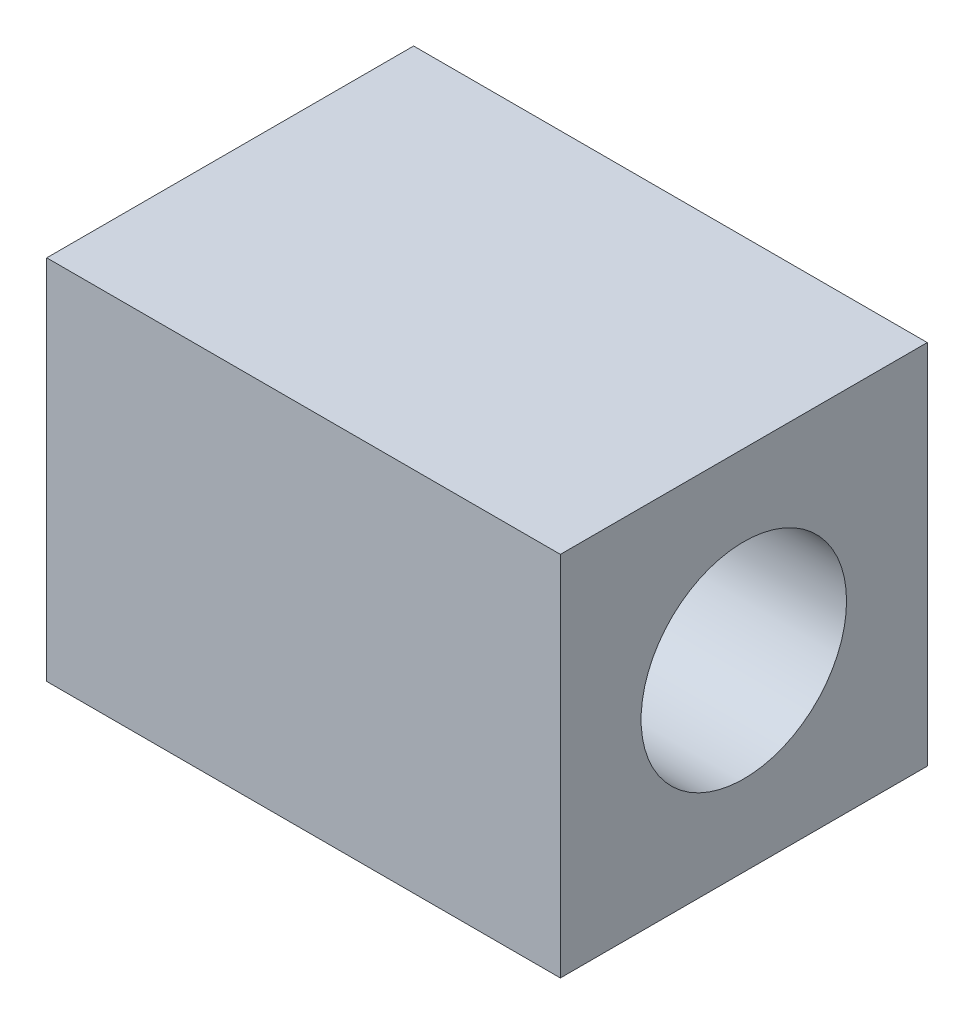
SolidWorks part; units mm, degrees
ref_plane "Front Plane" through (0, 0, 0) normal (0, 0, 1) x (1, 0, 0)
ref_plane "Top Plane" through (0, 0, 0) normal (0, 1, 0) x (1, 0, 0)
ref_plane "Right Plane" through (0, 0, 0) normal (1, 0, 0) x (0, 0, -1)
sketch "Sketch1" plane through (0, 0, 0) normal (1, 0, 0) x (0, 0, -1)
  line L1 (-15.875, 15.875) -> (15.875, 15.875)
  line L2 (-15.875, 15.875) -> (-15.875, -15.875)
  line L3 (-15.875, -15.875) -> (15.875, -15.875)
  line L4 (15.875, 15.875) -> (15.875, -15.875)
  line L5 (-15.875, 15.875) -> (15.875, -15.875) construction
  line L6 (-15.875, -15.875) -> (15.875, 15.875) construction
  circle A0 centre (0, 0) radius 8.89
  dimension "D1" = 17.78
  dimension "D2" = 31.75
  dimension "D3" = 31.75
extrude "Boss-Extrude1" add sketch "Sketch1" along normal mid plane 44.45
sketch "Sketch3" plane through (0, 15.875, 0) normal (0, 1, 0) x (1, 0, 0)
  line L0 (0, 15.875) -> (0, -15.875) construction
  line L1 (22.225, 15.875) -> (-22.225, 15.875) construction
  line L2 (22.225, -15.875) -> (-22.225, -15.875) construction
  line L3 (-22.225, 0) -> (22.225, 0) construction
  line L4 (-22.225, 15.875) -> (-22.225, -15.875) construction
  line L5 (22.225, 15.875) -> (22.225, -15.875) construction
